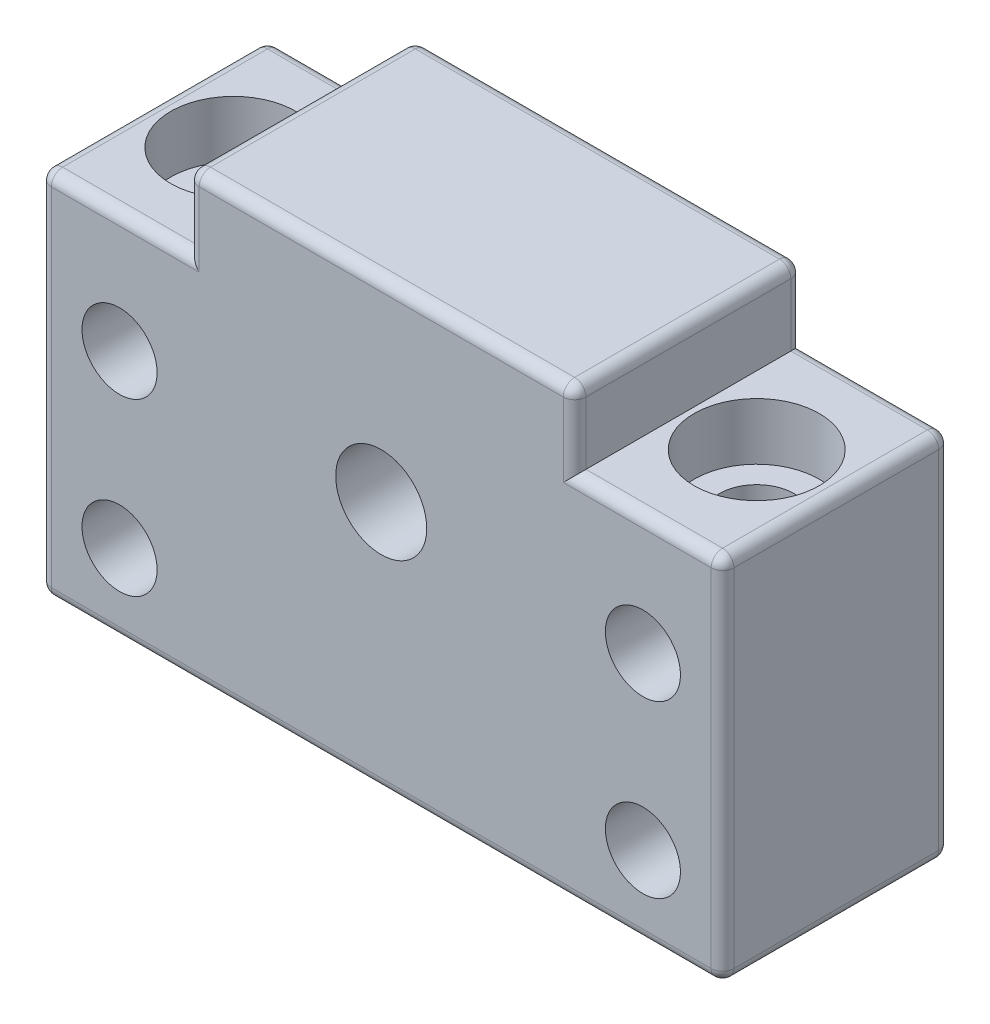
SolidWorks part; units mm, degrees
ref_plane "前视基准面" through (0, 0, 0) normal (0, 0, 1) x (1, 0, 0)
ref_plane "上视基准面" through (0, 0, 0) normal (0, 1, 0) x (1, 0, 0)
ref_plane "右视基准面" through (0, 0, 0) normal (1, 0, 0) x (0, 0, -1)
other "Configuration Table"
sketch "草图1" plane through (0, 0, 0) normal (0, 0, 1) x (1, 0, 0)
  line L0 (0, 19.5) -> (0, 16.25)
  line L1 (-30, 16.25) -> (30, 16.25)
  line L2 (-30, 16.25) -> (-30, -16.25)
  line L3 (-30, -16.25) -> (30, -16.25)
  line L4 (30, 16.25) -> (30, -16.25)
  line L5 (-30, 16.25) -> (30, -16.25) construction
  line L6 (-30, -16.25) -> (30, 16.25) construction
  line L7 (-17, 22.75) -> (17, 22.75)
  line L8 (-17, 22.75) -> (-17, 16.25)
  line L9 (-17, 16.25) -> (17, 16.25)
  line L10 (17, 22.75) -> (17, 16.25)
  line L11 (-17, 22.75) -> (17, 16.25) construction
  line L12 (-17, 16.25) -> (17, 22.75) construction
  line L13 (0, 16.25) -> (0, 0)
  line L14 (-23, 16.25) -> (-23, 5.75)
  line L15 (23, 16.25) -> (23, 5.75)
  circle A0 centre (0, 5.75) radius 4
  circle A2 centre (-23, 5.75) radius 3.3
  circle A3 centre (-23, -9.25) radius 3.3
  circle A4 centre (23, -9.25) radius 3.3
  circle A5 centre (23, 5.75) radius 3.3
  point P0 (0, 0)
  point P6 (0, 19.5)
  dimension "D5" = 6.6
  dimension "D6" = 6.6
  dimension "D11" = 8
  dimension "D1" = 60
  dimension "D2" = 32.5
  dimension "D3" = 6.5
  dimension "D4" = 34
  dimension "D7" = 22
  dimension "D8" = 15
  dimension "D9" = 7
  dimension "D10" = 22
extrude "凸台-拉伸1" add sketch "草图1" along normal blind 20
sketch "草图4" plane through (0, 16.25, 0) normal (0, 1, 0) x (1, 0, 0)
  line L1 (-30, -20) -> (-30, 0) construction
  line L2 (30, -20) -> (30, 0) construction
  line L3 (-30, -20) -> (-17, -20) construction
  line L4 (17, -20) -> (30, -20) construction
  circle A0 centre (-23, -10) radius 5.5
  circle A1 centre (23, -10) radius 5.5
  dimension "D1" = 11
  dimension "D2" = 11
  dimension "D3" = 7
  dimension "D4" = 7
  dimension "D5" = 10
  dimension "D6" = 10
extrude "切除-拉伸1" cut sketch "草图4" against normal blind 5 and the other way through all
fillet "圆角1" radius 1 1 edges at (-17, 22.75, 10)
fillet "圆角2" radius 1 1 edges at (17, 22.75, 10)
fillet "圆角4" radius 1 1 edges at (30, 16.25, 10)
fillet "圆角5" radius 1 1 edges at (-30, 16.25, 10)
fillet "圆角6" radius 1 5 edges at (-17, 19, 20) (0, 22.75, 20) (-16.7071, 22.4571, 20) (17, 19, 20) (16.7071, 22.4571, 20)
fillet "圆角7" radius 1 5 edges at (-17, 19, 0) (0, 22.75, 0) (-16.7071, 22.4571, 0) (17, 19, 0) (16.7071, 22.4571, 0)
fillet "圆角8" radius 1 4 edges at (-22.5, 16.25, 20) (-30, -0.5, 20) (-29.7071, 15.9571, 20) (-16.7071, 16.25, 19.7071)
fillet "圆角9" radius 1 4 edges at (16.7071, 16.25, 19.7071) (22.5, 16.25, 20) (30, -0.5, 20) (29.7071, 15.9571, 20)
fillet "圆角10" radius 1 4 edges at (16.7071, 16.25, 0.2929) (22.5, 16.25, 0) (30, -0.5, 0) (29.7071, 15.9571, 0)
fillet "圆角11" radius 1 4 edges at (-16.7071, 16.25, 0.2929) (-22.5, 16.25, 0) (-30, -0.5, 0) (-29.7071, 15.9571, 0)
fillet "圆角12" radius 1 8 edges at (-30, -16.25, 10) (0, -16.25, 20) (-29.7071, -16.25, 19.7071) (30, -16.25, 10) (29.7071, -16.25, 19.7071) (29.7071, -16.25, 0.2929) (0, -16.25, 0) (-29.7071, -16.25, 0.2929)
sketch "草图5" plane through (0, 11.25, 0) normal (0, 1, 0) x (1, 0, 0)
  circle A0 centre (-23, -10) radius 3.3
  circle A1 centre (23, -10) radius 3.3
  point P3 (-23, -10)
  point P6 (23, -10)
  dimension "D1" = 6.6
extrude "切除-拉伸2" cut sketch "草图5" against normal blind 89
